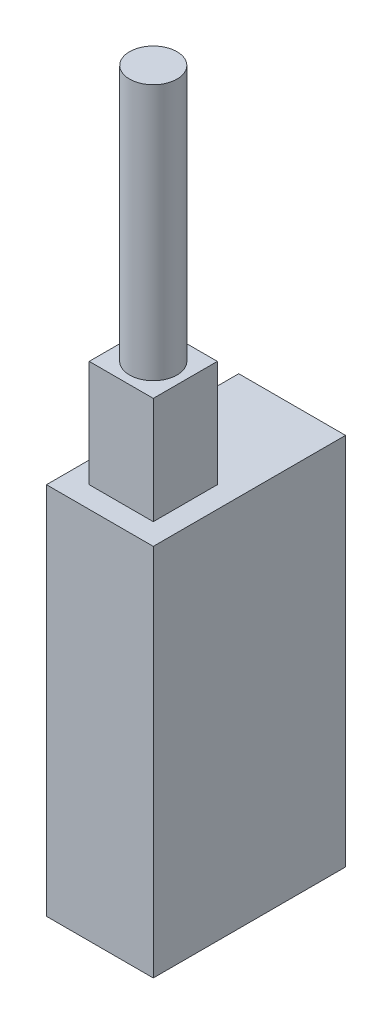
SolidWorks part; units mm, degrees
ref_plane "Front Plane" through (0, 0, 0) normal (0, 0, 1) x (1, 0, 0)
ref_plane "Top Plane" through (0, 0, 0) normal (0, 1, 0) x (1, 0, 0)
ref_plane "Right Plane" through (0, 0, 0) normal (1, 0, 0) x (0, 0, -1)
sketch "Sketch1" plane through (0, 0, 0) normal (0, 1, 0) x (1, 0, 0)
  line L1 (-10, -18) -> (10, -18)
  line L2 (-10, -18) -> (-10, 18)
  line L3 (-10, 18) -> (10, 18)
  line L4 (10, -18) -> (10, 18)
  line L5 (-10, -18) -> (10, 18) construction
  line L6 (-10, 18) -> (10, -18) construction
  point P0 (0, 0)
  dimension "D1" = 20
  dimension "D2" = 36
extrude "Boss-Extrude1" add sketch "Sketch1" along normal blind 70
sketch "Sketch2" plane through (0, 70, 0) normal (0, 1, 0) x (1, 0, 0)
  line L0 (-10, -18) -> (10, -18) construction
  line L1 (-6, -14) -> (6, -14)
  line L2 (-6, -14) -> (-6, -2)
  line L3 (-6, -2) -> (6, -2)
  line L4 (6, -14) -> (6, -2)
  line L5 (-6, -14) -> (6, -2) construction
  line L6 (-6, -2) -> (6, -14) construction
  point P0 (0, -8)
  point P8 (0, -18)
  dimension "D1" = 12
  dimension "D2" = 12
  dimension "D3" = 10
extrude "Boss-Extrude2" add sketch "Sketch2" along normal blind 20
sketch "Sketch3" plane through (0, 90, 0) normal (0, 1, 0) x (1, 0, 0)
  line L0 (-6, -2) -> (6, -14) construction
  line L1 (6, -2) -> (-6, -14) construction
  circle A0 centre (0, -8) radius 4.445
extrude "Boss-Extrude3" add sketch "Sketch3" along normal blind 48
